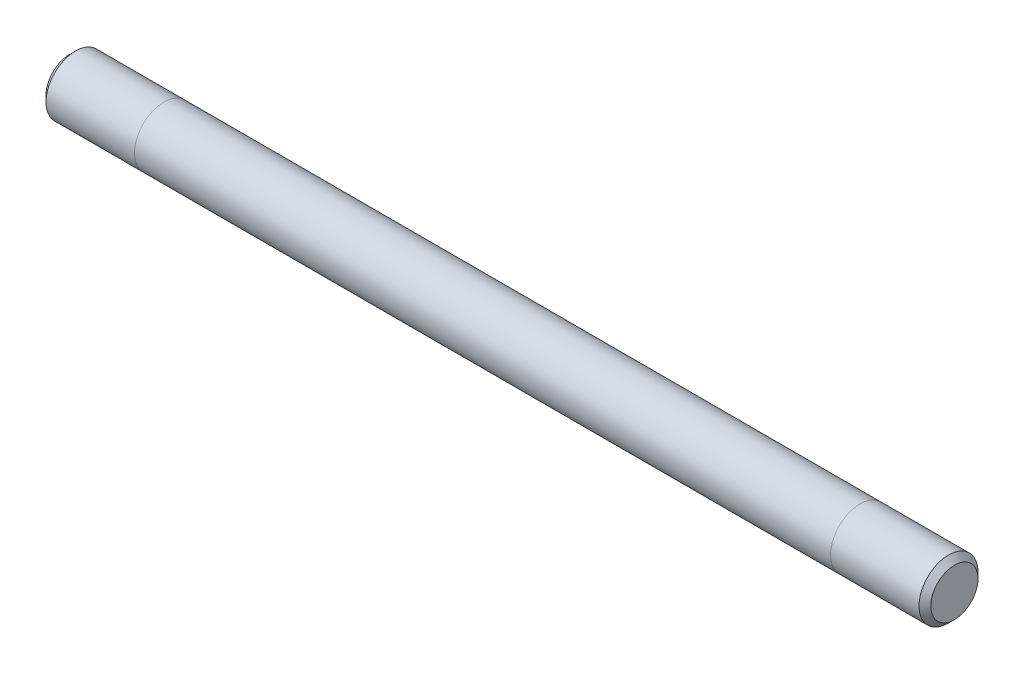
SolidWorks part; units mm, degrees
ref_plane "Ebene vorne" through (0, 0, 0) normal (0, 0, 1) x (1, 0, 0)
ref_plane "Ebene oben" through (0, 0, 0) normal (0, 1, 0) x (1, 0, 0)
ref_plane "Ebene rechts" through (0, 0, 0) normal (1, 0, 0) x (0, 0, -1)
sketch "Skizze1" plane through (0, 0, 0) normal (1, 0, 0) x (0, 0, -1)
  circle A0 centre (0, 0) radius 5
  dimension "D1" = 10
extrude "Aufsatz-Linear austragen1" add sketch "Skizze1" along normal mid plane 150
ref_plane "Ebene1" through (59, 0, 0) normal (1, 0, 0) x (0, 0, -1)
ref_plane "Ebene2" through (-59, 0, 0) normal (-1, 0, 0) x (0, 0, 1)
split line "Trennlinie1"
cosmetic thread "Gewindedarstellung1" parameters "D2"=8.891
cosmetic thread "Gewindedarstellung2" parameters "D2"=8.891
chamfer "Fase1" distance 1 angle 45 2 edges at (-75, 0, -5) (75, 0, -5)
